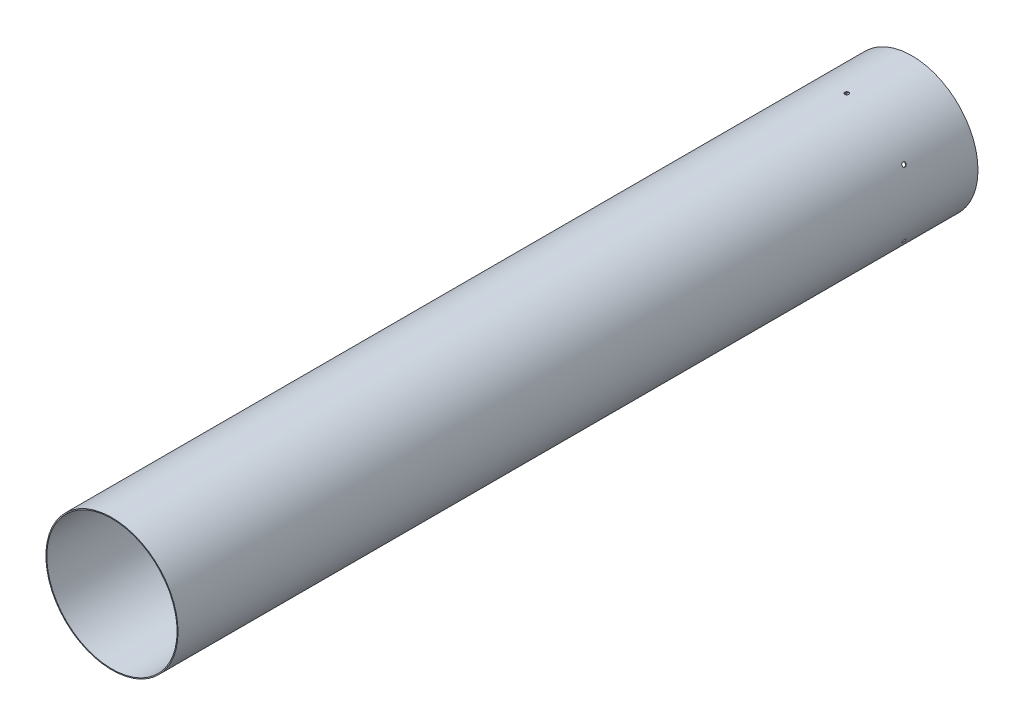
SolidWorks part; units mm, degrees
ref_plane "Front Plane" through (0, 0, 0) normal (0, 0, 1) x (1, 0, 0)
ref_plane "Top Plane" through (0, 0, 0) normal (0, 1, 0) x (1, 0, 0)
ref_plane "Right Plane" through (0, 0, 0) normal (1, 0, 0) x (0, 0, -1)
sketch "Sketch1" plane through (0, 0, 0) normal (0, 0, 1) x (1, 0, 0)
  circle A0 centre (0, 0) radius 79.375
  circle A1 centre (0, 0) radius 80.518
  dimension "D1" = 158.75
  dimension "D2" = 1.143
extrude "Boss-Extrude1" add sketch "Sketch1" along normal blind 974.725
ref_plane "Plane1" through (0, 80.518, 0) normal (0, 1, 0) x (1, 0, 0)
sketch "Sketch2" plane through (0, 80.518, 0) normal (0, 1, 0) x (1, 0, 0)
  line L0 (79.375, 0) -> (-79.375, 0) construction
  point P0 (0, -79.375)
  dimension "D1" = 79.375
hole_wizard "#10 (0.1935) Diameter Hole1" positions "Sketch3" profile "Sketch4" hole size "#10" standard "ANSI Inch"
sketch "Sketch3" plane through (0, 80.518, 0) normal (0, 1, 0) x (1, 0, 0)
  point P0 (0, -79.375)
sketch "Sketch4" plane through (0, 80.518, 79.375) normal (1, 0, 0) x (0, 0, 1)
  line L0 (0, 0) -> (0, 1.143)
  line L1 (0, 1.143) -> (2.4574, 1.143)
  line L2 (2.4574, 1.143) -> (2.4574, 0)
  line L5 (2.4574, 0) -> (0, 0)
  line L11 (0, -6.35) -> (0, 107.95) construction
  dimension "Thru Hole Dia." = 4.9149
  dimension "Thru Hole Depth" = 1.143
pattern_circular "CirPattern1" count 6 over 360 about axis through (0, 0, 0) along (0, 0, 1) of "#10 (0.1935) Diameter Hole1"
